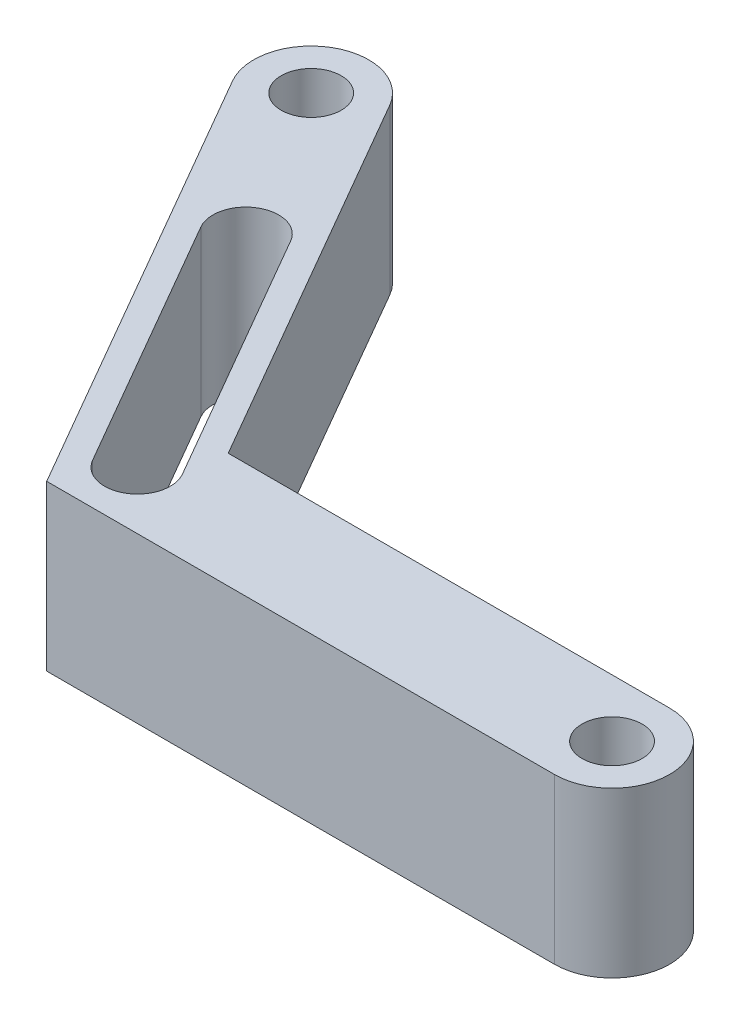
SolidWorks part; units mm, degrees
material "ABS"
ref_plane "Ebene vorne" through (0, 0, 0) normal (0, 0, 1) x (1, 0, 0)
ref_plane "Ebene oben" through (0, 0, 0) normal (0, 1, 0) x (1, 0, 0)
ref_plane "Ebene rechts" through (0, 0, 0) normal (1, 0, 0) x (0, 0, -1)
sketch "Skizze2" plane through (0, 0, 0) normal (0, 1, 0) x (1, 0, 0)
  line L1 (0, 3.5) -> (-26.8468, 3.5)
  line L2 (-26.8468, 3.5) -> (-40.2702, 26.75)
  line L4 (-46.3324, 23.25) -> (-30.8882, -3.5)
  line L5 (-30.8882, -3.5) -> (0, -3.5)
  line L6 (0, 0) -> (-28.8675, 0) construction
  line L7 (-43.3013, 25) -> (-28.8675, 0) construction
  line L8 (-43.3013, 25) -> (0, 0) construction
  arc A4 (0, 3.5) -> (0, -3.5) centre (0, 0) cw
  arc A5 (-40.2702, 26.75) -> (-46.3324, 23.25) centre (-43.3013, 25) ccw
  circle A6 centre (-43.3013, 25) radius 1.825
  circle A7 centre (0, 0) radius 1.825
  dimension "D3" = 50
  dimension "D4" = 60
  dimension "D5" = 3.65
  dimension "D6" = 3.65
  dimension "D1" = 7
  dimension "D2" = 7
extrude "Aufsatz-Linear austragen1" add sketch "Skizze2" along normal blind 10
sketch "Skizze3" plane through (0, 10, 0) normal (0, 1, 0) x (1, 0, 0)
  line L0 (0, 0) -> (-43.3013, 25) construction
sketch "Skizze4" plane through (0, 10, 0) normal (0, 1, 0) x (1, 0, 0)
  line L0 (-37.8675, 15.5885) -> (-28.8675, 0) construction
  line L1 (-36.1355, 16.5885) -> (-27.1355, 1)
  line L2 (-39.5996, 14.5885) -> (-30.5996, -1)
  line L3 (-26.8468, 3.5) -> (-40.2702, 26.75) construction
  line L4 (-46.3324, 23.25) -> (-30.8882, -3.5) construction
  arc A0 (-36.1355, 16.5885) -> (-39.5996, 14.5885) centre (-37.8675, 15.5885) ccw
  arc A1 (-30.5996, -1) -> (-27.1355, 1) centre (-28.8675, 0) ccw
  point P2 (-33.3675, 7.7942)
  dimension "D1" = 18
  dimension "D2" = 4
extrude "Schnitt-Linear austragen1" cut sketch "Skizze4" against normal through all
